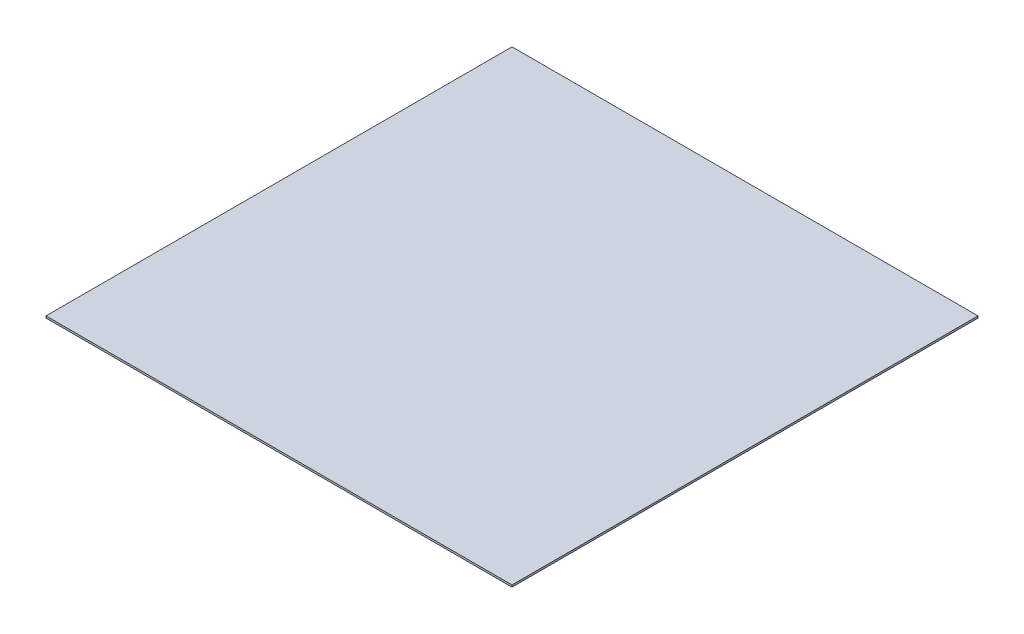
SolidWorks part; units mm, degrees
ref_plane "Front Plane" through (0, 0, 0) normal (0, 0, 1) x (1, 0, 0)
ref_plane "Top Plane" through (0, 0, 0) normal (0, 1, 0) x (1, 0, 0)
ref_plane "Right Plane" through (0, 0, 0) normal (1, 0, 0) x (0, 0, -1)
sketch "Sketch1" plane through (0, 0, 0) normal (0, 1, 0) x (1, 0, 0)
  line L1 (60, -60) -> (-60, -60)
  line L2 (60, -60) -> (60, 60)
  line L3 (60, 60) -> (-60, 60)
  line L4 (-60, -60) -> (-60, 60)
  line L5 (60, -60) -> (-60, 60) construction
  line L6 (60, 60) -> (-60, -60) construction
  point P0 (0, 0)
  dimension "D1" = 120
extrude "Extrude1" add sketch "Sketch1" along normal blind 0.5
